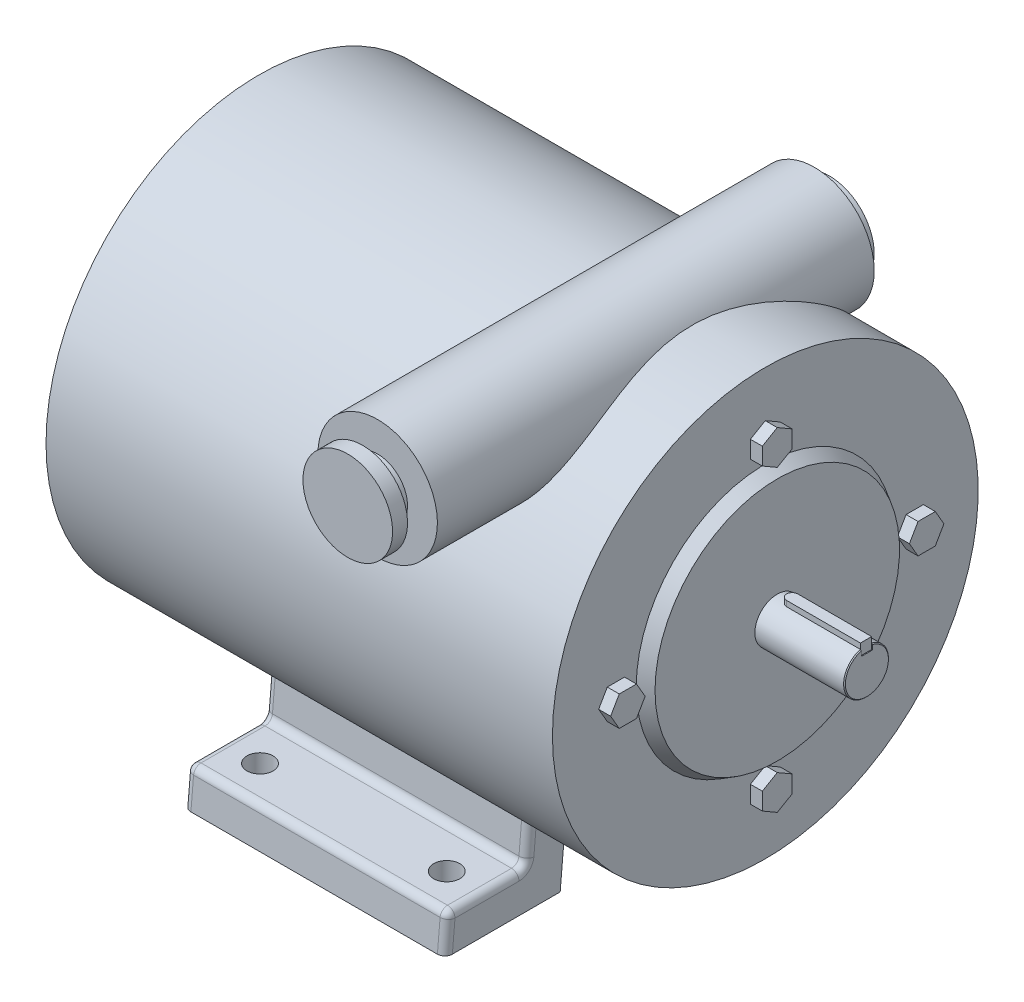
SolidWorks part; units mm, degrees
ref_plane "Front Plane" through (0, 0, 0) normal (0, 0, 1) x (1, 0, 0)
ref_plane "Top Plane" through (0, 0, 0) normal (0, 1, 0) x (1, 0, 0)
ref_plane "Right Plane" through (0, 0, 0) normal (1, 0, 0) x (0, 0, -1)
sketch "Sketch1" plane through (0, 0, 0) normal (1, 0, 0) x (0, 0, -1)
  circle A0 centre (0, 0) radius 9.525
  dimension "Dim A" = 19.05
extrude "Boss-Extrude1" add sketch "Sketch1" along normal mid plane 301.625
ref_plane "Plane1" through (-112.7125, 0, 0) normal (-1, 0, 0) x (0, 0, 1)
ref_plane "Plane2" through (-107.6325, 0, 0) normal (-1, 0, 0) x (0, 0, 1)
sketch "Sketch2" plane through (-107.6325, 0, 0) normal (-1, 0, 0) x (0, 0, 1)
  circle A0 centre (0, 0) radius 90.4875
  dimension "Dim Z" = 180.975
extrude "Boss-Extrude2" add sketch "Sketch2" against normal blind 12.7
sketch "Sketch3" plane through (0, 0, 0) normal (0, 0, 1) x (1, 0, 0)
  line L0 (-150.8125, 0) -> (0, 0) construction
  line L1 (-150.8125, 9.525) -> (-150.8125, -9.525) construction
  line L2 (-94.9325, 0) -> (-94.9325, 90.4875)
  line L3 (-94.9325, -90.4875) -> (-94.9325, 90.4875) construction
  line L5 (-94.9325, 90.4875) -> (107.6325, 90.4875)
  line L7 (0, 0) -> (107.6325, 0) construction
  line L9 (107.6325, 90.4875) -> (107.6325, 0)
  line L11 (-150.8125, -9.525) -> (-107.6325, -9.525) construction
  line L12 (-107.6325, 6.985) -> (-107.6325, -6.985) construction
  line L13 (107.6325, 0) -> (150.8125, 0) construction
  line L14 (150.8125, -9.525) -> (150.8125, 9.525) construction
  line L15 (-94.9325, 0) -> (107.6325, 0)
revolve "Revolve1" add sketch "Sketch3" angle 360 about L13
ref_plane "Plane3" through (58.7375, 0, 0) normal (1, 0, 0) x (0, 0, -1)
sketch "Sketch4" plane through (58.7375, 0, 0) normal (1, 0, 0) x (0, 0, -1)
  line L0 (-87.3125, -107.95) -> (-38.296, -107.95)
  line L1 (0, 0) -> (0, -107.95) construction
  line L2 (-87.3125, -107.95) -> (-85.9236, -92.075)
  line L3 (-85.9236, -92.075) -> (-52.9036, -92.075)
  line L4 (87.3125, -107.95) -> (85.9236, -92.075)
  line L5 (52.9036, -92.075) -> (85.9236, -92.075)
  line L6 (-52.9036, -92.075) -> (-51.3656, -74.4954)
  line L7 (-38.296, -107.95) -> (-36.1105, -82.97)
  line L8 (-52.9036, -92.075) -> (-37.0286, -93.4639) construction
  line L9 (-37.0286, -93.4639) -> (-52.9036, -92.075) construction
  line L10 (37.0286, -93.4639) -> (52.9036, -92.075) construction
  line L11 (52.9036, -92.075) -> (37.0286, -93.4639) construction
  line L12 (38.296, -107.95) -> (36.1105, -82.97)
  line L13 (52.9036, -92.075) -> (51.3656, -74.4954)
  line L14 (38.296, -107.95) -> (87.3125, -107.95)
  line L15 (-51.3656, -74.4954) -> (-36.1105, -82.97)
  line L16 (36.1105, -82.97) -> (51.3656, -74.4954)
  circle A0 centre (0, 0) radius 90.4875 construction
  point P8 (0, -92.075)
  dimension "D2" = 33.02
  dimension "D1" = 85
  dimension "Dim N" = 174.625
  dimension "Dim T" = 107.95
  dimension "Dim Y" = 15.875
extrude "Boss-Extrude3" add sketch "Sketch4" against normal blind 111.125
ref_plane "Plane6" through (83.185, 0, 0) normal (1, 0, 0) x (0, 0, -1)
fillet "Fillet1" radius 3.175 18 edges at (3.175, -92.075, 85.9236) (58.7375, -92.075, 69.4136) (58.7375, -100.0125, -86.6181) (-52.3875, -100.0125, -86.6181) (-52.3875, -92.075, 69.4136) (-52.3875, -100.0125, 86.6181) (58.7375, -100.0125, 86.6181) (-52.3875, -92.075, -69.4136) (58.7375, -92.075, -69.4136) (3.175, -92.075, -85.9236) (-52.3875, -83.2852, -52.1346) (58.7375, -83.2852, -52.1346) (3.175, -92.075, -52.9036) (58.7375, -83.2852, 52.1346) (-52.3875, -83.2852, 52.1346) (3.175, -92.075, 52.9036) (3.175, -82.97, -36.1105) (3.175, -82.97, 36.1105)
sketch "Sketch7" plane through (0, -92.075, 0) normal (0, 1, 0) x (1, 0, 0)
  line L0 (58.7375, -55.813) -> (58.7375, -83.0143) construction
  line L1 (-36.5125, -70.6437) -> (42.8625, -70.6437) construction
  line L2 (0, 0) -> (150.8125, 0) construction
  line L3 (150.8125, -9.525) -> (150.8125, 9.525) construction
  circle A0 centre (42.8625, -70.6437) radius 5.5562
  circle A1 centre (-36.5125, -70.6437) radius 5.5562
  circle A2 centre (42.8625, 70.6437) radius 5.5562
  circle A3 centre (-36.5125, 70.6438) radius 5.5562
  dimension "Dim U" = 11.1125
  dimension "Dim G_4" = 15.875
  dimension "Dim F_4" = 79.375
  dimension "Dim O_4" = 141.2875
extrude "DD5ALS AND DD15A" cut sketch "Sketch7" against normal through all
chamfer "Chamfer1" distance 0.381 angle 45 2 edges at (150.8125, 0, -9.525) (-150.8125, 0, -9.525)
sketch "Sketch10" plane through (-150.8125, 0, 0) normal (-1, 0, 0) x (0, 0, 1)
  line L0 (-2.3812, 9.525) -> (2.3813, 9.525) construction
  line L1 (-2.3812, 9.2225) -> (-2.3812, 9.525)
  line L2 (-2.3812, 9.2225) -> (-2.3812, 6.8072)
  line L3 (-2.3812, 6.8072) -> (2.3813, 6.8072)
  line L4 (2.3813, 9.2225) -> (2.3813, 6.8072)
  line L5 (-2.3812, 9.525) -> (2.3813, 9.525)
  line L6 (2.3813, 9.525) -> (2.3813, 9.2225)
  line L7 (0, 6.8072) -> (0, 0) construction
  circle A0 centre (0, 0) radius 9.525 construction
  circle A1 centre (0, 0) radius 9.525 construction
  dimension "Dim K" = 4.7625
  dimension "Dim Keyway depth" = 2.7178
extrude "Cut-Extrude8" cut sketch "Sketch10" against normal offset from surface (31.75 mm away) 6.35 up to plane "Plane1"
mirror "Mirror2" about plane through (0, 0, 0) normal (1, 0, 0) of "Cut-Extrude8"
sketch "Sketch11" plane through (0, 6.8072, 0) normal (0, 1, 0) x (1, 0, 0)
  line L0 (-150.4315, 2.3812) -> (-150.4315, -2.3813)
  line L1 (-150.4315, -2.3813) -> (-119.0625, -2.3813)
  line L2 (-119.0625, 2.3812) -> (-150.4315, 2.3812)
  arc A0 (-119.0625, -2.3813) -> (-119.0625, 2.3812) centre (-119.0625, 0) ccw
extrude "Boss-Extrude4" add sketch "Sketch11" along normal blind 4.7625 separate body
mirror "Mirror3" about plane through (0, 0, 0) normal (1, 0, 0) of bodies 109
ref_plane "Plane4" through (0, 0, 125.4125) normal (0, 0, 1) x (1, 0, 0)
sketch "Sketch12" plane through (0, 0, 125.4125) normal (0, 0, 1) x (1, 0, 0)
  line L0 (-49.2125, -107.95) -> (55.5625, -107.95) construction
  line L1 (150.8125, -9.144) -> (150.8125, 8.8285) construction
  circle A0 centre (55.5625, 76.2) radius 25.4
  dimension "Dim S" = 50.8
  dimension "Dim M" = 184.15
  dimension "Dim D" = 95.25
extrude "Boss-Extrude5" add sketch "Sketch12" against normal blind 204.724 separate body
ref_axis "Axis1" through (55.5625, 76.2, -79.3115) along (0, 0, 1)
ref_plane "Plane5" through (55.5625, 0, 0) normal (1, 0, 0) x (0, 0, -1)
sketch "Sketch13" plane through (55.5625, 0, 0) normal (1, 0, 0) x (0, 0, -1)
  line L0 (-125.4125, 95.25) -> (-119.0625, 95.25)
  line L1 (-125.4125, 71.5962) -> (-125.4125, -71.5962) construction
  line L2 (-119.0625, 95.25) -> (-119.0625, 88.9)
  line L3 (-119.0625, 88.9) -> (-112.7125, 88.9)
  line L4 (-112.7125, 88.9) -> (-112.7125, 101.6)
  line L5 (79.3115, 101.6) -> (-125.4125, 101.6) construction
  line L6 (-112.7125, 101.6) -> (-125.4125, 101.6)
  line L7 (-125.4125, 101.6) -> (-125.4125, 95.25)
  line L8 (72.9615, 101.6) -> (72.9615, 95.25)
  line L9 (72.9615, 95.25) -> (79.3115, 95.25)
  line L10 (79.3115, 50.8) -> (79.3115, 101.6) construction
  line L11 (79.3115, 95.25) -> (79.3115, 101.6)
  line L12 (79.3115, 101.6) -> (72.9615, 101.6)
  dimension "D1" = 6.35
  dimension "D2" = 6.35
  dimension "D3" = 6.35
  dimension "D4" = 6.35
revolve "Cut-Revolve1" cut sketch "Sketch13" angle 360 about axis through (55.5625, 76.2, -79.3115) along (0, 0, 1)
sketch "Sketch16" plane through (-112.7125, 0, 0) normal (-1, 0, 0) x (0, 0, 1)
  line L0 (56.1677, 0) -> (59.8338, -6.35)
  line L1 (0, 56.1677) -> (6.35, 59.8338)
  line L2 (6.35, 59.8338) -> (6.35, 67.1662)
  line L3 (6.35, 67.1662) -> (0, 70.8323)
  line L4 (0, 70.8323) -> (-6.35, 67.1662)
  line L5 (-6.35, 67.1662) -> (-6.35, 59.8338)
  line L6 (-6.35, 59.8338) -> (0, 56.1677)
  line L7 (59.8338, -6.35) -> (67.1662, -6.35)
  line L8 (67.1662, -6.35) -> (70.8323, 0)
  line L9 (70.8323, 0) -> (67.1662, 6.35)
  line L10 (67.1662, 6.35) -> (59.8338, 6.35)
  line L11 (59.8338, 6.35) -> (56.1677, 0)
  line L12 (0, -56.1677) -> (-6.35, -59.8338)
  line L13 (-6.35, -59.8338) -> (-6.35, -67.1662)
  line L14 (-6.35, -67.1662) -> (0, -70.8323)
  line L15 (0, -70.8323) -> (6.35, -67.1662)
  line L16 (6.35, -67.1662) -> (6.35, -59.8338)
  line L17 (6.35, -59.8338) -> (0, -56.1677)
  line L18 (-56.1677, 0) -> (-59.8338, 6.35)
  line L19 (-59.8338, 6.35) -> (-67.1662, 6.35)
  line L20 (-67.1662, 6.35) -> (-70.8323, 0)
  line L21 (-70.8323, 0) -> (-67.1662, -6.35)
  line L22 (-67.1662, -6.35) -> (-59.8338, -6.35)
  line L23 (-59.8338, -6.35) -> (-56.1677, 0)
  line L24 (-63.5, 0) -> (63.5, 0) construction
  circle A0 centre (0, 63.5) radius 6.35 construction
  circle A2 centre (63.5, 0) radius 6.35 construction
  circle A3 centre (0, -63.5) radius 6.35 construction
  circle A4 centre (-63.5, 0) radius 6.35 construction
  dimension "D1" = 12.7
  dimension "D3" = 127
  dimension "D2" = 4
extrude "Boss-Extrude6" add sketch "Sketch16" against normal up to surface (5.08 mm away) separate body up to face at (-107.6325, 0, 90.4875)
sketch "Sketch18" plane through (-107.6325, 0, 0) normal (-1, 0, 0) x (0, 0, 1)
  line L0 (0, 0) -> (0, 54.8977) construction
  line L1 (0, 54.8977) -> (0, 56.1677) construction
  circle A0 centre (0, 0) radius 54.8977
  dimension "D1" = 1.27
extrude "Boss-Extrude7" add sketch "Sketch18" along normal up to surface (5.08 mm away) draft 30 separate body
mirror "Mirror4" about plane through (0, 0, 0) normal (1, 0, 0) of bodies 119 120 117 118 116
combine bodies "Combine1" operation type add bodies to combine 112 109 114 120 119 117 118 116 111 121 123 122 125 124
